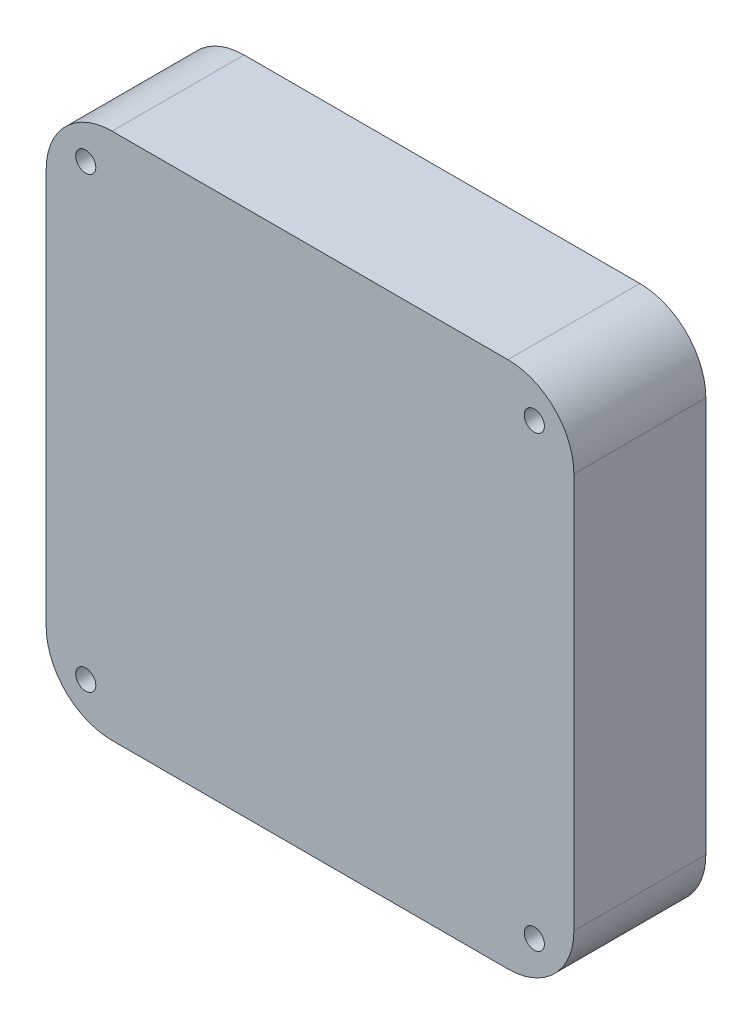
SolidWorks part; units mm, degrees
ref_plane "Front Plane" through (0, 0, 0) normal (0, 0, 1) x (1, 0, 0)
ref_plane "Top Plane" through (0, 0, 0) normal (0, 1, 0) x (1, 0, 0)
ref_plane "Right Plane" through (0, 0, 0) normal (1, 0, 0) x (0, 0, -1)
sketch "Sketch1" plane through (0, 0, 0) normal (0, 0, 1) x (1, 0, 0)
  line L1 (0, 0) -> (40, 0)
  line L2 (0, 0) -> (0, 40)
  line L3 (0, 40) -> (40, 40)
  line L4 (40, 0) -> (40, 40)
  dimension "D1" = 40
  dimension "D2" = 40
extrude "Boss-Extrude1" add sketch "Sketch1" along normal blind 10
hole_wizard "Ø3.0mm Dowel Hole1" positions "Sketch3" profile "Sketch4" hole size "Ø3.0" standard "ANSI Metric" end condition through all
sketch "Sketch3" plane through (0, 0, 10) normal (0, 0, 1) x (1, 0, 0)
  line L0 (40, 40) -> (0, 40) construction
  line L1 (0, 40) -> (0, 0) construction
  point P0 (3, 37)
  dimension "D1" = 3
  dimension "D2" = 3
sketch "Sketch4" plane through (3, 37, 10) normal (1, 0, 0) x (0, -1, 0)
  line L0 (0, 0) -> (0, 10)
  line L1 (0, 10) -> (0.762, 10)
  line L2 (0.762, 10) -> (0.762, 0)
  line L5 (0.762, 0) -> (0, 0)
  line L11 (0, -6.35) -> (0, 107.95) construction
  dimension "Thru Hole Dia." = 1.524
  dimension "Thru Hole Depth" = 10
ref_plane "Plane1" through (20, 0, 0) normal (-1, 0, 0) x (0, 0, 1)
mirror "Mirror1" about plane through (20, 0, 0) normal (-1, 0, 0) of "Ø3.0mm Dowel Hole1"
ref_plane "Plane2" through (0, 20, 0) normal (0, 1, 0) x (1, 0, 0)
mirror "Mirror2" about plane through (0, 20, 0) normal (0, 1, 0) of "Mirror1", "Ø3.0mm Dowel Hole1"
fillet "Fillet1" radius 5 4 edges at (40, 40, 5) (40, 0, 5) (0, 0, 5) (0, 40, 5)
